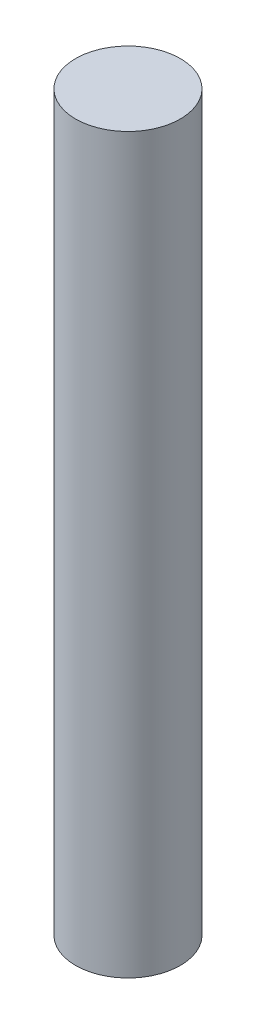
SolidWorks part; units mm, degrees
ref_plane "Front Plane" through (0, 0, 0) normal (0, 0, 1) x (1, 0, 0)
ref_plane "Top Plane" through (0, 0, 0) normal (0, 1, 0) x (1, 0, 0)
ref_plane "Right Plane" through (0, 0, 0) normal (1, 0, 0) x (0, 0, -1)
sketch "Sketch2" plane through (0, 0, 0) normal (0, 1, 0) x (1, 0, 0)
  circle A0 centre (0, 0) radius 12.7
  dimension "D1" = 25.4
extrude "Boss-Extrude3" add sketch "Sketch2" along normal blind 177.8
